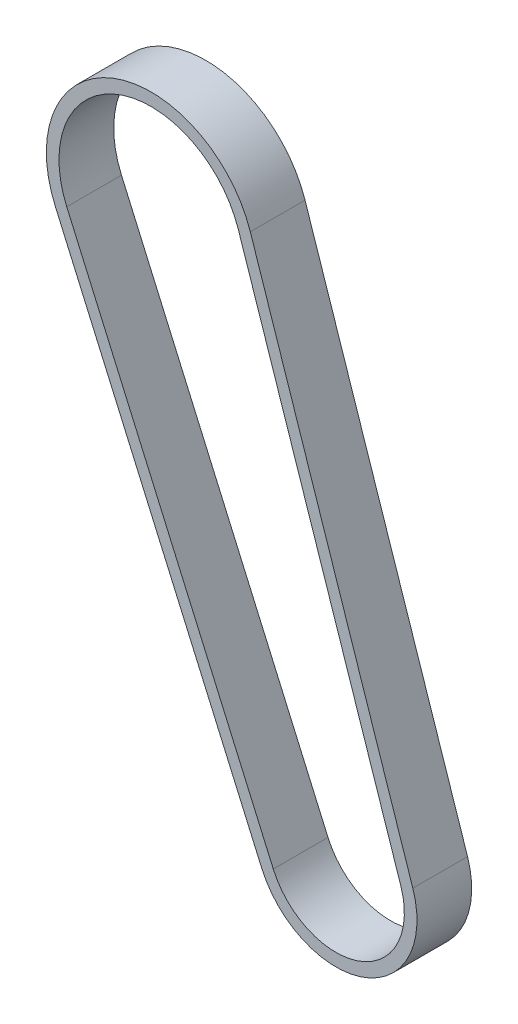
SolidWorks part; units mm, degrees
ref_plane "Front Plane" through (0, 0, 0) normal (0, 0, 1) x (1, 0, 0)
ref_plane "Top Plane" through (0, 0, 0) normal (0, 1, 0) x (1, 0, 0)
ref_plane "Right Plane" through (0, 0, 0) normal (1, 0, 0) x (0, 0, -1)
sketch "Sketch2" plane through (0, 0, 0) normal (0, 0, 1) x (1, 0, 0)
  line L0 (0, 0) -> (1, 0) construction
  line L1 (0, 0) -> (0, 1) construction
  line L2 (19.2433, 1.3097) -> (51.9109, -96.6239)
  line L3 (26.2687, -106.5074) -> (-15.2445, -11.9833)
  arc A0 (-15.2445, -11.9833) -> (19.2433, 1.3097) centre (1.6939, -4.5442) cw
  arc A1 (51.9109, -96.6239) -> (26.2687, -106.5074) centre (38.8626, -100.9764) cw
extrude "Extrude-Thin1" add sketch "Sketch2" along normal up to surface (11 mm away) thin thin type one direction wall 2.54
